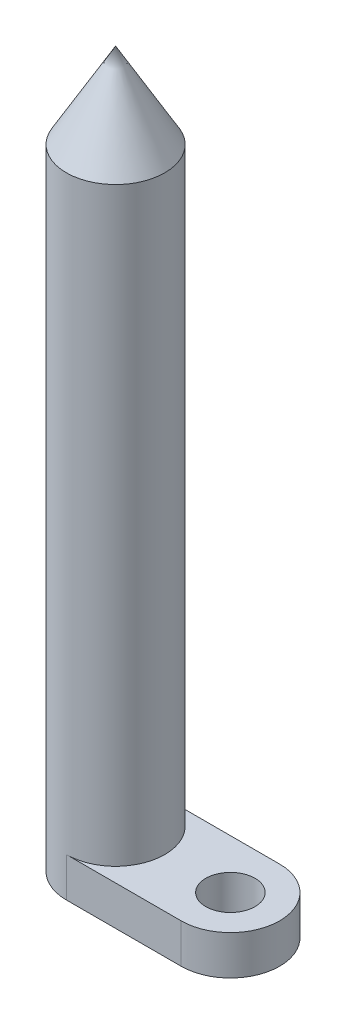
SolidWorks part; units mm, degrees
ref_plane "Front Plane" through (0, 0, 0) normal (0, 0, 1) x (1, 0, 0)
ref_plane "Top Plane" through (0, 0, 0) normal (0, 1, 0) x (1, 0, 0)
ref_plane "Right Plane" through (0, 0, 0) normal (1, 0, 0) x (0, 0, -1)
sketch "Sketch1" plane through (0, 0, 0) normal (0, 1, 0) x (1, 0, 0)
  line L0 (0, 15) -> (35, 15)
  line L1 (0, -15) -> (35, -15)
  arc A0 (0, 15) -> (0, -15) centre (0, 0) ccw
  arc A1 (35, -15) -> (35, 15) centre (35, 0) ccw
  circle A2 centre (35, 0) radius 7.5
  dimension "D2" = 30
  dimension "D3" = 35
  dimension "D4" = 15
extrude "Boss-Extrude1" add sketch "Sketch1" along normal blind 12
sketch "Sketch2" plane through (0, 12, 0) normal (0, 1, 0) x (1, 0, 0)
  circle A0 centre (0, 0) radius 15
  dimension "D1" = 30
extrude "Boss-Extrude2" add sketch "Sketch2" along normal blind 180
sketch "Sketch3" plane through (0, 0, 0) normal (1, 0, 0) x (0, 0, -1)
  line L0 (0, -19.3303) -> (0, 210.0801) construction
  line L1 (15, 192) -> (0, 192)
  line L2 (15, 192) -> (-15, 192) construction
  line L3 (0, 192) -> (0, 217.9808)
  line L4 (0, 217.9808) -> (15, 192)
  dimension "D1" = 30
revolve "Revolve1" add sketch "Sketch3" angle 360 about L0
